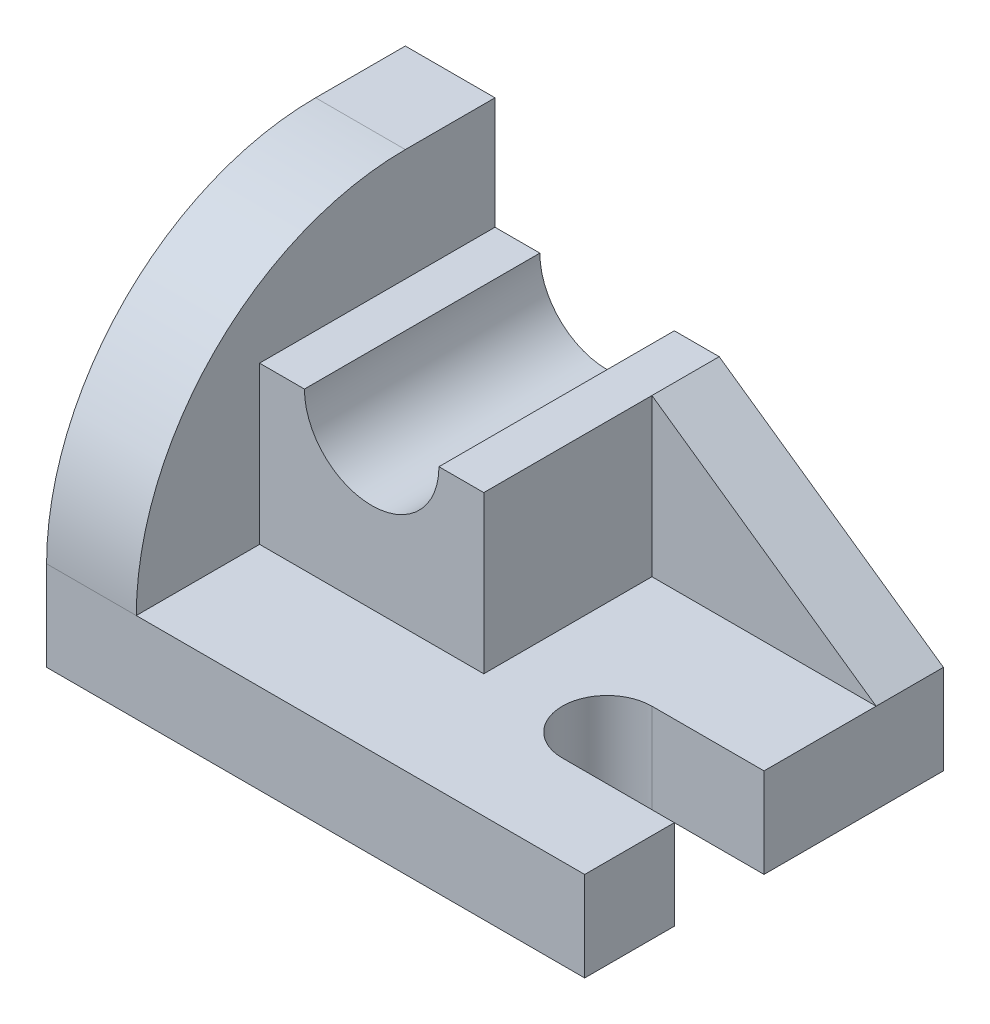
SolidWorks part; units mm, degrees
ref_plane "Front Plane" through (0, 0, 0) normal (0, 0, 1) x (1, 0, 0)
ref_plane "Top Plane" through (0, 0, 0) normal (0, 1, 0) x (1, 0, 0)
ref_plane "Right Plane" through (0, 0, 0) normal (1, 0, 0) x (0, 0, -1)
sketch "Sketch5" plane through (0, 0, 0) normal (0, 1, 0) x (1, 0, 0)
  line L1 (0, 0) -> (96, 0)
  line L2 (0, 0) -> (0, 64)
  line L3 (0, 64) -> (96, 64)
  line L4 (96, 0) -> (96, 16)
  line L5 (96, 16) -> (76, 16)
  line L6 (96, 32) -> (76, 32)
  line L7 (96, 32) -> (96, 64)
  arc A1 (76, 32) -> (76, 16) centre (76, 24) ccw
  point P7 (86, 24)
  dimension "D1" = 96
  dimension "D2" = 64
  dimension "D3" = 16
  dimension "D4" = 20
extrude "Boss-Extrude3" add sketch "Sketch5" along normal blind 16
sketch "Sketch6" plane through (0, 0, 0) normal (-1, 0, 0) x (0, 0, 1)
  line L0 (-64, 0) -> (-64, 64)
  line L1 (-64, 64) -> (-48, 64)
  line L2 (0, 16) -> (0, 0)
  line L3 (0, 0) -> (-64, 0)
  arc A0 (-48, 64) -> (0, 16) centre (-48, 16) cw
  dimension "D2" = 48
  dimension "D1" = 64
extrude "Boss-Extrude4" add sketch "Sketch6" against normal blind 16
sketch "Sketch7" plane through (0, 0, -64) normal (0, 0, -1) x (-1, 0, 0)
  line L1 (-16, 16) -> (-56, 16)
  line L2 (-16, 16) -> (-16, 44)
  line L3 (-16, 44) -> (-56, 44)
  line L4 (-56, 16) -> (-56, 44)
  circle A0 centre (-36, 44) radius 12
  line M9 (-16, 64) -> (-16, 16)
  line M10 (-16, 16) -> (-96, 16)
  dimension "D3" = 24
  dimension "D1" = 28
  dimension "D2" = 40
extrude "Boss-Extrude5" add sketch "Sketch7" against normal blind 42 contours A0 L3 L4 M10 M9
sketch "Sketch8" plane through (0, 0, -64) normal (0, 0, -1) x (-1, 0, 0)
  line L0 (-96, 16) -> (-56, 44)
  line L1 (-56, 44) -> (-56, 16)
  line L2 (-56, 16) -> (-96, 16)
extrude "Boss-Extrude6" add sketch "Sketch8" against normal blind 12
